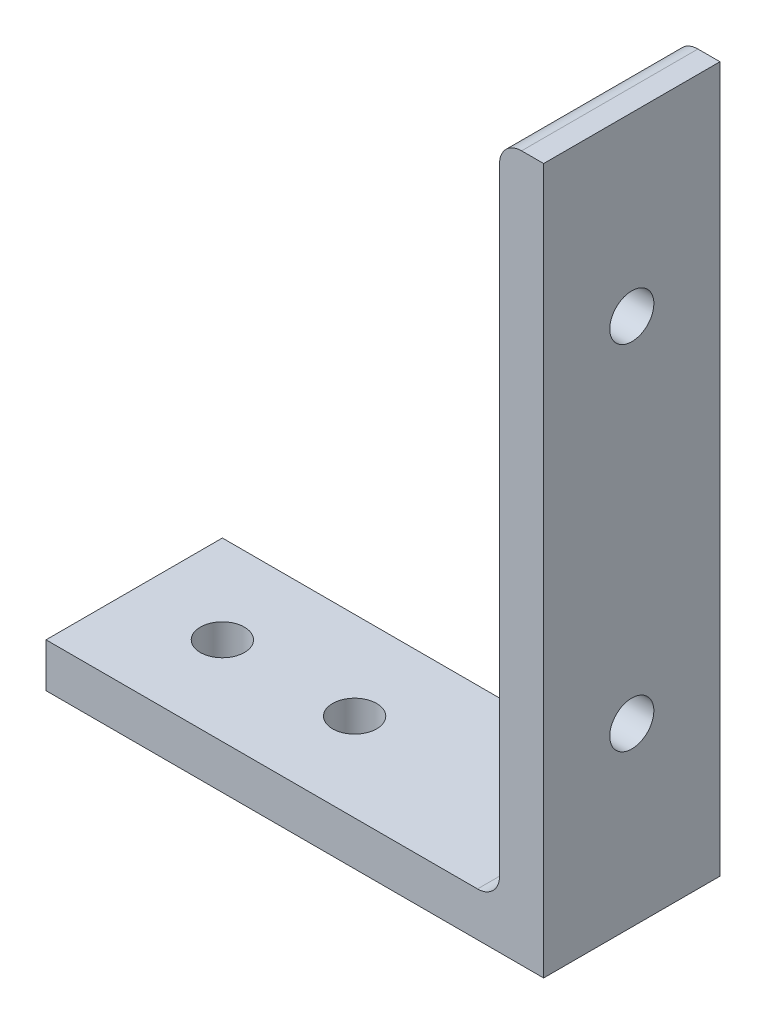
SolidWorks part; units mm, degrees
ref_plane "Front Plane" through (0, 0, 0) normal (0, 0, 1) x (1, 0, 0)
ref_plane "Top Plane" through (0, 0, 0) normal (0, 1, 0) x (1, 0, 0)
ref_plane "Right Plane" through (0, 0, 0) normal (1, 0, 0) x (0, 0, -1)
sketch "Sketch2" plane through (0, 0, 0) normal (0, 0, 1) x (1, 0, 0)
  line L0 (-38.1, 0) -> (38.1, 0)
  line L1 (38.1, 0) -> (38.1, 101.6)
  line L2 (38.1, 101.6) -> (31.75, 101.6) construction
  line L3 (31.75, 98.425) -> (31.75, 9.525)
  line L4 (28.575, 6.35) -> (-34.925, 6.35)
  line L5 (-38.1, 0) -> (-38.1, 6.35) construction
  line L6 (34.925, 101.6) -> (38.1, 101.6)
  line L7 (-38.1, 3.175) -> (-38.1, 0)
  arc A0 (31.75, 98.425) -> (34.925, 101.6) centre (34.925, 98.425) cw
  arc A1 (-38.1, 3.175) -> (-34.925, 6.35) centre (-34.925, 3.175) cw
  arc A2 (31.75, 9.525) -> (28.575, 6.35) centre (28.575, 9.525) cw
  dimension "Vert" = 101.6
  dimension "Horz" = 76.2
  dimension "Thickness" = 6.35
extrude "Boss-Extrude1" add sketch "Sketch2" along normal mid plane 25.4
ref_plane "Contact Plane 1" through (0, 6.35, 0) normal (0, 1, 0) x (1, 0, 0)
ref_plane "Contact Plane 2" through (31.75, 0, 0) normal (-1, 0, 0) x (0, 0, 1)
sketch "Sketch3" plane through (38.1, 0, 0) normal (1, 0, 0) x (0, 0, -1)
  line L0 (0, 101.6) -> (0, 0) construction
  line L4 (12.7, 0) -> (12.7, 101.6)
  line L5 (12.7, 101.6) -> (-12.7, 101.6)
  line L6 (-12.7, 101.6) -> (-12.7, 0)
  line L7 (-12.7, 0) -> (12.7, 0)
  line L8 (12.7, 0) -> (12.7, 101.6) construction
  line L9 (12.7, 101.6) -> (-12.7, 101.6) construction
  line L10 (-12.7, 101.6) -> (-12.7, 0) construction
  line L11 (-12.7, 0) -> (12.7, 0) construction
  circle A0 centre (0, 76.2) radius 3.175
  circle A1 centre (0, 25.4) radius 3.175
  dimension "D4" = 6.35
  dimension "D2" = 25.4
  dimension "D3" = 25.4
  dimension "D1" = 0
extrude "Cut-Extrude1" cut sketch "Sketch3" against normal up to next
sketch "Sketch4" plane through (-38.1, 0, 0) normal (-1, 0, 0) x (0, 0, 1)
  line L1 (-12.7, 0) -> (15.8074, 0)
  line L2 (-12.7, 0) -> (-12.7, 9.1504)
  line L3 (-12.7, 9.1504) -> (15.8074, 9.1504)
  line L4 (15.8074, 0) -> (15.8074, 9.1504)
extrude "Cut-Extrude2" cut sketch "Sketch4" against normal blind 4.5237
sketch "Sketch5" plane through (0, 6.35, 0) normal (0, 1, 0) x (1, 0, 0)
  line L0 (28.575, 0) -> (-33.5763, 0) construction
  line L4 (28.575, 12.7) -> (-33.5763, 12.7)
  line L5 (-33.5763, 12.7) -> (-33.5763, -12.7)
  line L6 (-33.5763, -12.7) -> (28.575, -12.7)
  line L7 (28.575, -12.7) -> (28.575, 12.7)
  line L8 (28.575, 12.7) -> (-33.5763, 12.7) construction
  line L9 (-33.5763, 12.7) -> (-33.5763, -12.7) construction
  line L10 (-33.5763, -12.7) -> (28.575, -12.7) construction
  line L11 (28.575, -12.7) -> (28.575, 12.7) construction
  circle A0 centre (-1.8263, 0) radius 3.175
  circle A1 centre (-20.8763, 0) radius 3.175
  dimension "D2" = 6.35
  dimension "D3" = 31.75
  dimension "D4" = 12.7
  dimension "D1" = 0
extrude "Cut-Extrude3" cut sketch "Sketch5" against normal through all
